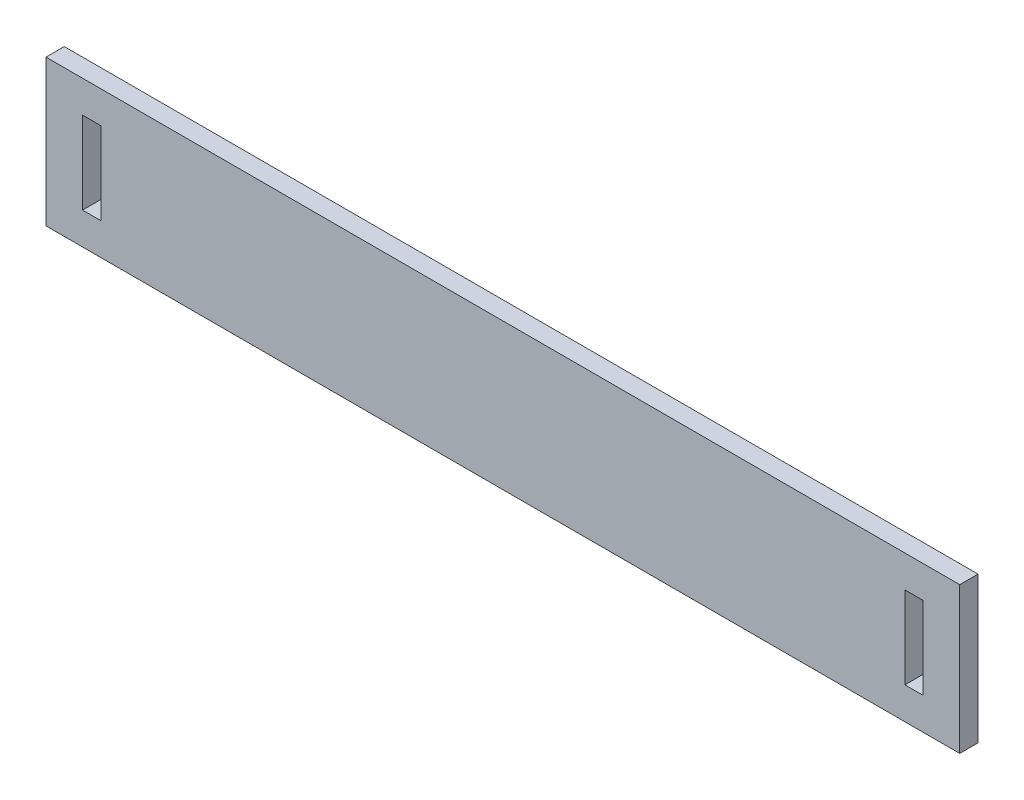
SolidWorks part; units mm, degrees
ref_plane "Front Plane" through (0, 0, 0) normal (0, 0, 1) x (1, 0, 0)
ref_plane "Top Plane" through (0, 0, 0) normal (0, 1, 0) x (1, 0, 0)
ref_plane "Right Plane" through (0, 0, 0) normal (1, 0, 0) x (0, 0, -1)
sketch "Sketch2" plane through (0, 0, 0) normal (0, 0, 1) x (1, 0, 0)
  line L1 (-62.1174, 42.8701) -> (137.8826, 42.8701)
  line L2 (-62.1174, 42.8701) -> (-62.1174, 10.8701)
  line L3 (-62.1174, 10.8701) -> (137.8826, 10.8701)
  line L4 (137.8826, 42.8701) -> (137.8826, 10.8701)
extrude "Boss-Extrude1" add sketch "Sketch2" along normal blind 4
sketch "Sketch3" plane through (0, 0, 4) normal (0, 0, 1) x (1, 0, 0)
  line L1 (-54.1174, 35.8701) -> (-50.1174, 35.8701)
  line L2 (-54.1174, 35.8701) -> (-54.1174, 17.8701)
  line L3 (-54.1174, 17.8701) -> (-50.1174, 17.8701)
  line L4 (-50.1174, 35.8701) -> (-50.1174, 17.8701)
  line L5 (125.8826, 35.8701) -> (129.8826, 35.8701)
  line L6 (125.8826, 35.8701) -> (125.8826, 17.8701)
  line L7 (125.8826, 17.8701) -> (129.8826, 17.8701)
  line L8 (129.8826, 35.8701) -> (129.8826, 17.8701)
  line L9 (137.8826, 42.8701) -> (-62.1174, 42.8701) construction
  line L11 (-62.1174, 42.8701) -> (-62.1174, 10.8701) construction
  dimension "D1" = 7
  dimension "D2" = 18
  dimension "D3" = 7
  dimension "D4" = 4
  dimension "D5" = 18
  dimension "D6" = 4
  dimension "D7" = 176
  dimension "D8" = 8
extrude "Cut-Extrude1" cut sketch "Sketch3" against normal blind 4
